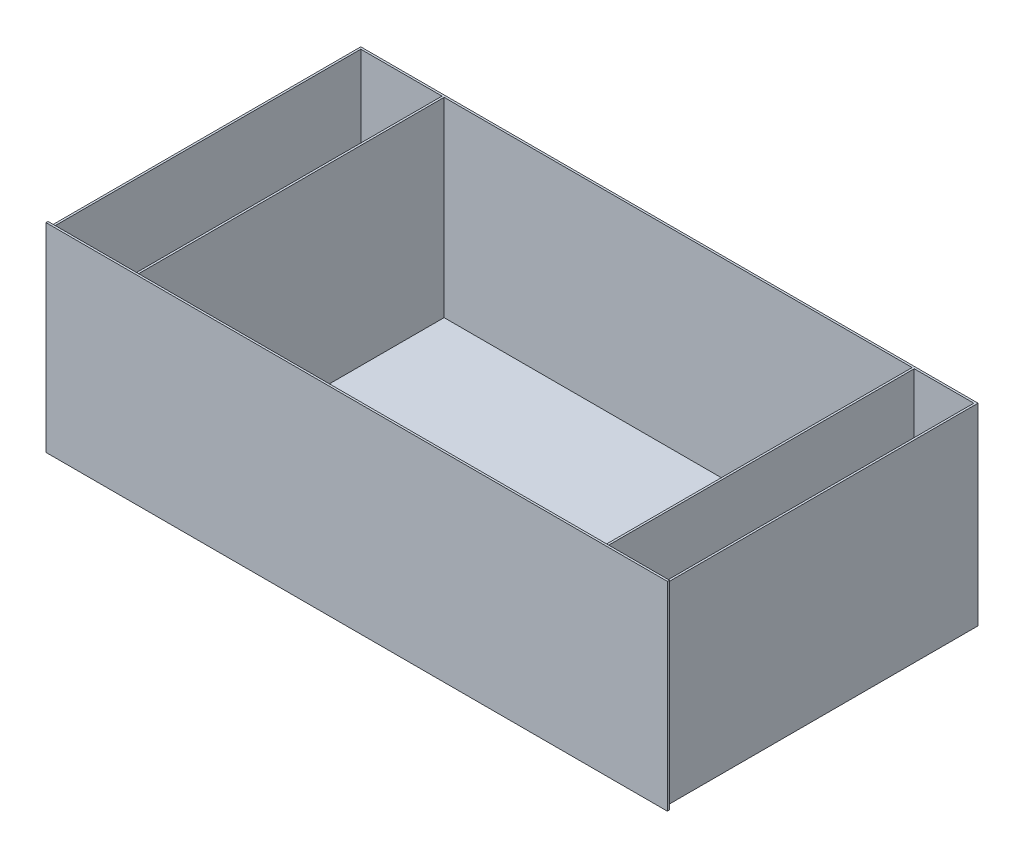
SolidWorks part; units mm, degrees
material "PVC Rigid"
ref_plane "Front Plane" through (0, 0, 0) normal (0, 0, 1) x (1, 0, 0)
ref_plane "Top Plane" through (0, 0, 0) normal (0, 1, 0) x (1, 0, 0)
ref_plane "Right Plane" through (0, 0, 0) normal (1, 0, 0) x (0, 0, -1)
sketch "Sketch1" plane through (0, 0, 0) normal (0, 0, 1) x (1, 0, 0)
  line L1 (-604, 193.5) -> (604, 193.5)
  line L2 (-604, 193.5) -> (-604, -193.5)
  line L3 (-604, -193.5) -> (604, -193.5)
  line L4 (604, 193.5) -> (604, -193.5)
  line L5 (-604, 193.5) -> (604, -193.5) construction
  line L6 (-604, -193.5) -> (604, 193.5) construction
  point P0 (0, 0)
extrude "Boss-Extrude1" add sketch "Sketch1" along normal blind 4
ref_plane "Plane1" through (0, -187.5, 0) normal (0, 1, 0) x (1, 0, 0)
sketch "Sketch2" plane through (0, -187.5, 0) normal (0, 1, 0) x (1, 0, 0)
  line L0 (-600, 0) -> (600, 0)
  line L2 (604, 0) -> (-604, 0) construction
  line L3 (600, 0) -> (600, 604)
  line L4 (600, 604) -> (-600, 604)
  line L5 (-600, 604) -> (-600, 0)
  point P8 (0, 0)
extrude "Boss-Extrude2" add sketch "Sketch2" along normal blind 375 contours L5 L0 L3 L4
sketch "Sketch3" plane through (0, 187.5, 0) normal (0, 1, 0) x (1, 0, 0)
  line L0 (600, 604) -> (-600, 604) construction
  line L1 (-600, 604) -> (-600, 0) construction
  line L2 (-596, 600) -> (-596, 4)
  line L3 (-596, 4) -> (-438, 4)
  line L4 (-438, 4) -> (-438, 600)
  line L5 (-438, 600) -> (-596, 600)
  line L6 (-434, 600) -> (476, 600)
  line L7 (476, 600) -> (476, 4)
  line L8 (476, 4) -> (-434, 4)
  line L9 (-434, 4) -> (-434, 600)
  line L10 (480, 600) -> (596, 600)
  line L11 (596, 600) -> (596, 4)
  line L12 (596, 4) -> (480, 4)
  line L13 (480, 4) -> (480, 600)
  point P0 (-596, 600)
  point P9 (-434, 600)
  point P14 (480, 600)
  dimension "D1" = 4
  dimension "D2" = 4
  dimension "D3" = 4
  dimension "D4" = 4
extrude "Cut-Extrude1" cut sketch "Sketch3" against normal blind 371
sketch "Sketch4" plane through (0, 0, 4) normal (0, 0, 1) x (1, 0, 0)
  circle A0 centre (0, 0) radius 7.5 construction
